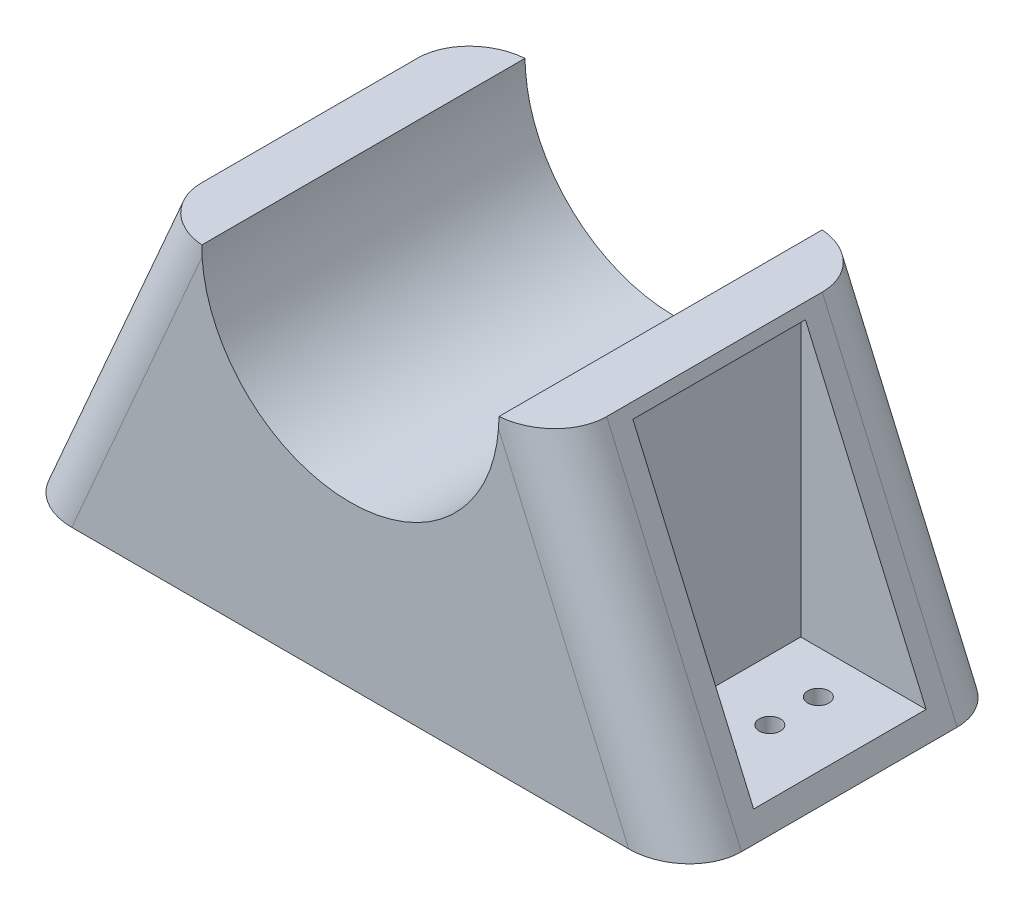
SolidWorks part; units mm, degrees
ref_plane "Front Plane" through (0, 0, 0) normal (0, 0, 1) x (1, 0, 0)
ref_plane "Top Plane" through (0, 0, 0) normal (0, 1, 0) x (1, 0, 0)
ref_plane "Right Plane" through (0, 0, 0) normal (1, 0, 0) x (0, 0, -1)
sketch "Sketch1" plane through (0, 0, 0) normal (0, 0, 1) x (1, 0, 0)
  circle A0 centre (0, 0) radius 35
  circle A1 centre (0, 0) radius 47.7
  dimension "D1" = 70
  dimension "D2" = 12.7
extrude "Boss-Extrude1" add sketch "Sketch1" along normal blind 76.2
sketch "Sketch2" plane through (0, 0, 76.2) normal (0, 0, 1) x (1, 0, 0)
  line L0 (-50.9777, 0) -> (54.1903, 0)
extrude "Cut-Extrude1" cut sketch "Sketch2" against normal through all and the other way through all
sketch "Sketch3" plane through (0, 0, 0) normal (0, 0, -1) x (-1, 0, 0)
  line L0 (-47.7, 0) -> (47.7, 0)
  line L5 (-47.7, 0) -> (-47.7, -47.5073)
  line L6 (47.7, 0) -> (47.7, -47.5073)
  line L7 (-47.7, -47.5073) -> (47.7, -47.5073)
  line L8 (-47.7, -47.5073) -> (47.7, -47.5073)
  line L9 (-47.7, -47.5073) -> (-47.7, -72.9073)
  line L10 (47.7, -47.5073) -> (47.7, -72.9073)
  line L11 (-47.7, -72.9073) -> (47.7, -72.9073)
  arc A0 (-47.7, 0) -> (47.7, 0) centre (0, 0) ccw construction
  arc M3 (-47.7, 0) -> (47.7, 0) centre (0, 0) ccw
  dimension "D1" = 25.4
extrude "Boss-Extrude2" add sketch "Sketch3" against normal blind 76.2 contours L5 L7 M3 | L7 L6 M3 | L9 L11 L10 L7 M3
sketch "Sketch4" plane through (0, 0, 0) normal (0, 0, -1) x (-1, 0, 0)
  line L0 (47.7, 0) -> (47.7, -72.9073)
  line L1 (47.7, 0) -> (79.45, -72.9073)
  line L2 (79.45, -72.9073) -> (47.7, -72.9073)
  dimension "D1" = 31.75
ref_plane "Plane1" through (47.7, 0, 0) normal (1, 0, 0) x (0, 0, -1)
sketch "Sketch5" plane through (0, 0, 0) normal (0, 0, -1) x (-1, 0, 0)
  line L0 (-47.7, 0) -> (-47.7, -72.9073)
  line L1 (-47.7, -72.9073) -> (-79.45, -72.9073)
  line L2 (-79.45, -72.9073) -> (-47.7, 0)
  dimension "D1" = 31.75
extrude "Boss-Extrude4" add sketch "Sketch5" against normal blind 76.2
fillet "Fillet2" radius 12.7 2 edges at (63.575, -36.4536, 0) (63.575, -36.4536, 76.2)
sketch "Sketch6" plane through (47.7, 0, 0) normal (1, 0, 0) x (0, 0, -1)
  line L0 (-58.42, -2.54) -> (-58.42, -67.8273)
  line L1 (-58.42, -2.54) -> (-17.78, -2.54)
  line L2 (-58.42, -67.8273) -> (-17.78, -67.8273)
  line L3 (-17.78, -2.54) -> (-17.78, -67.8273)
  line L4 (-63.5, -72.9073) -> (-12.7, -72.9073) construction
  line L5 (-63.5, 0) -> (-12.7, 0) construction
  line L6 (-12.7, -72.9073) -> (-12.7, 0) construction
  line L7 (-63.5, 0) -> (-63.5, -72.9073) construction
  dimension "D1" = 5.08
  dimension "D2" = 2.54
  dimension "D3" = 5.08
  dimension "D4" = 5.08
extrude "Cut-Extrude3" cut sketch "Sketch6" along normal blind 101.6
sketch "Sketch7" plane through (0, -67.8273, 0) normal (0, 1, 0) x (1, 0, 0)
  line L0 (77.2377, -17.78) -> (77.2377, -58.42) construction
  line L1 (77.2377, -58.42) -> (48.8061, -58.42) construction
  circle A0 centre (61.9977, -50.8) radius 2.5
  dimension "D1" = 15.24
  dimension "D2" = 7.62
  dimension "D3" = 5
extrude "Cut-Extrude4" cut sketch "Sketch7" against normal through all both and the other way through all
pattern_linear "LPattern1" count 3 spacing 11.43 along (0, 0, -1) of "Cut-Extrude4"
ref_plane "Plane2" through (-47.7, 0, 0) normal (-1, 0, 0) x (0, 0, 1)
extrude "Boss-Extrude5" add sketch "Sketch4" against normal blind 76.2
fillet "Fillet3" radius 12.7 2 edges at (-63.575, -36.4536, 0) (-63.575, -36.4536, 76.2)
sketch "Sketch8" plane through (-47.7, 0, 0) normal (-1, 0, 0) x (0, 0, 1)
  line L0 (17.78, -2.54) -> (58.42, -2.54)
  line L1 (17.78, -2.54) -> (17.78, -67.8273)
  line L2 (58.42, -2.54) -> (58.42, -67.8273)
  line L3 (17.78, -67.8273) -> (58.42, -67.8273)
  line L4 (63.5, -72.9073) -> (63.5, 0) construction
  line L5 (12.7, 0) -> (12.7, -72.9073) construction
  line L6 (63.5, -72.9073) -> (12.7, -72.9073) construction
  line L7 (12.7, 0) -> (63.5, 0) construction
  dimension "D1" = 5.08
  dimension "D2" = 5.08
  dimension "D3" = 5.08
  dimension "D4" = 2.54
extrude "Cut-Extrude5" cut sketch "Sketch8" along normal blind 76.2
sketch "Sketch9" plane through (0, -67.8273, 0) normal (0, 1, 0) x (1, 0, 0)
  line L0 (-77.2377, -58.42) -> (-47.7, -58.42) construction
  line L1 (-77.2377, -58.42) -> (-77.2377, -17.78) construction
  circle A0 centre (-61.9977, -50.8) radius 2.5
  dimension "D1" = 7.62
  dimension "D2" = 15.24
  dimension "D3" = 5
extrude "Cut-Extrude6" cut sketch "Sketch9" against normal through all both and the other way through all
pattern_linear "LPattern2" count 3 spacing 12.62 along (0, 0, -1) of "Cut-Extrude6"
